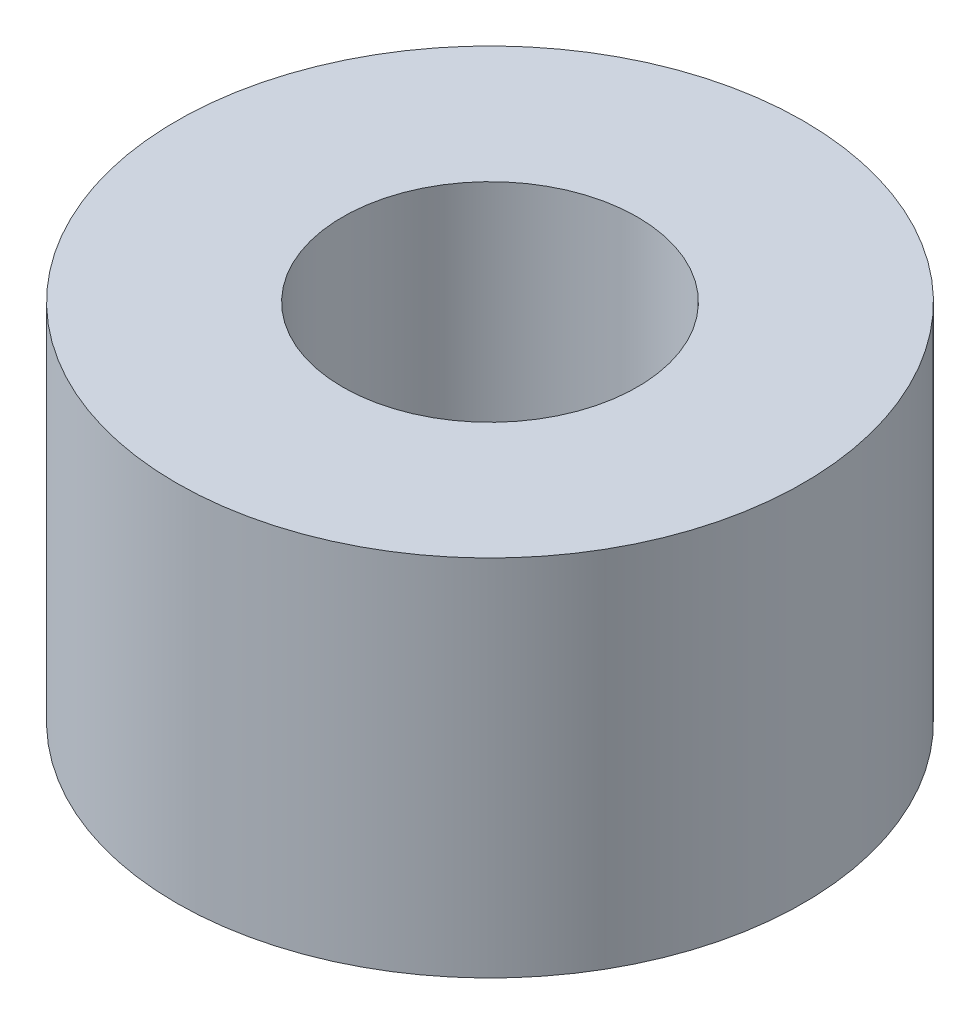
SolidWorks part; units mm, degrees
ref_plane "Front Plane" through (0, 0, 0) normal (0, 0, 1) x (1, 0, 0)
ref_plane "Top Plane" through (0, 0, 0) normal (0, 1, 0) x (1, 0, 0)
ref_plane "Right Plane" through (0, 0, 0) normal (1, 0, 0) x (0, 0, -1)
sketch "Sketch1" plane through (0, 0, 0) normal (0, 1, 0) x (1, 0, 0)
  circle A0 centre (0, 0) radius 2.5
  circle A1 centre (0, 0) radius 1.175
  dimension "D1" = 5
  dimension "D2" = 2.35
extrude "Boss-Extrude1" add sketch "Sketch1" along normal blind 2.9
